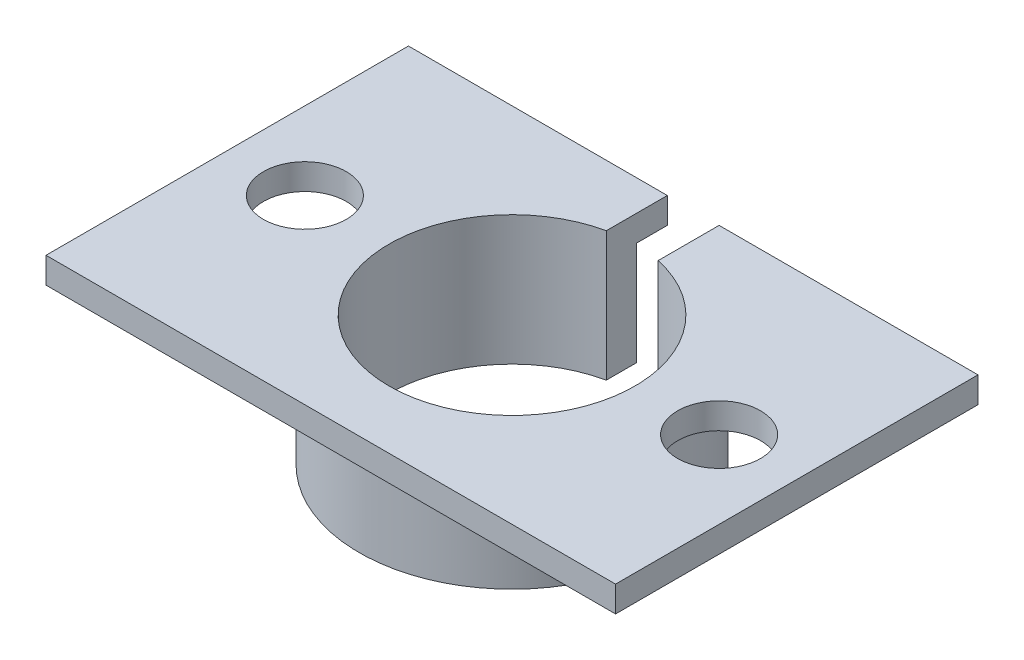
SolidWorks part; units mm, degrees
ref_plane "前视基准面" through (0, 0, 0) normal (0, 0, 1) x (1, 0, 0)
ref_plane "上视基准面" through (0, 0, 0) normal (0, 1, 0) x (1, 0, 0)
ref_plane "右视基准面" through (0, 0, 0) normal (1, 0, 0) x (0, 0, -1)
sketch "草图1" plane through (0, 0, 0) normal (0, 1, 0) x (1, 0, 0)
  line L0 (0, 0) -> (0, 7) construction
  line L1 (-11, 7) -> (11, 7)
  line L2 (-11, 7) -> (-11, -7)
  line L3 (-11, -7) -> (11, -7)
  line L4 (11, 7) -> (11, -7)
  line L5 (0, 0) -> (11, 0) construction
  circle A0 centre (0, 0) radius 5.9 construction
  dimension "D1" = 11.8
  dimension "D2" = 14
  dimension "D3" = 22
extrude "凸台-拉伸1" add sketch "草图1" along normal blind 1
sketch "草图2" plane through (0, 1, 0) normal (0, 1, 0) x (1, 0, 0)
  circle A0 centre (0, 0) radius 4.75
  dimension "D1" = 9.5
extrude "切除-拉伸1" cut sketch "草图2" against normal through all
sketch "草图3" plane through (0, 0, 0) normal (0, -1, 0) x (-1, 0, 0)
  circle A0 centre (0, 0) radius 5.9
  circle A1 centre (0, 0) radius 4.75
  dimension "D1" = 11.8
extrude "凸台-拉伸2" add sketch "草图3" along normal blind 4
sketch "草图4" plane through (0, 1, 0) normal (0, 1, 0) x (1, 0, 0)
  line L0 (8, 0) -> (0, 0) construction
  line L1 (0, 0) -> (-8, 0) construction
  circle A0 centre (8, 0) radius 1.6
  circle A1 centre (-8, 0) radius 1.6
  dimension "D2" = 3.2
  dimension "D1" = 16
extrude "切除-拉伸2" cut sketch "草图4" against normal blind 1
sketch "草图5" plane through (0, 1, 0) normal (0, 1, 0) x (1, 0, 0)
  line L0 (0, 0) -> (0, 7.9092) construction
  line L1 (1, 0.0084) -> (-1, 0.0084)
  line L2 (1, 0.0084) -> (1, 7.9092)
  line L3 (1, 7.9092) -> (-1, 7.9092)
  line L4 (-1, 0.0084) -> (-1, 7.9092)
  dimension "D1" = 2
extrude "切除-拉伸3" cut sketch "草图5" against normal blind 10
